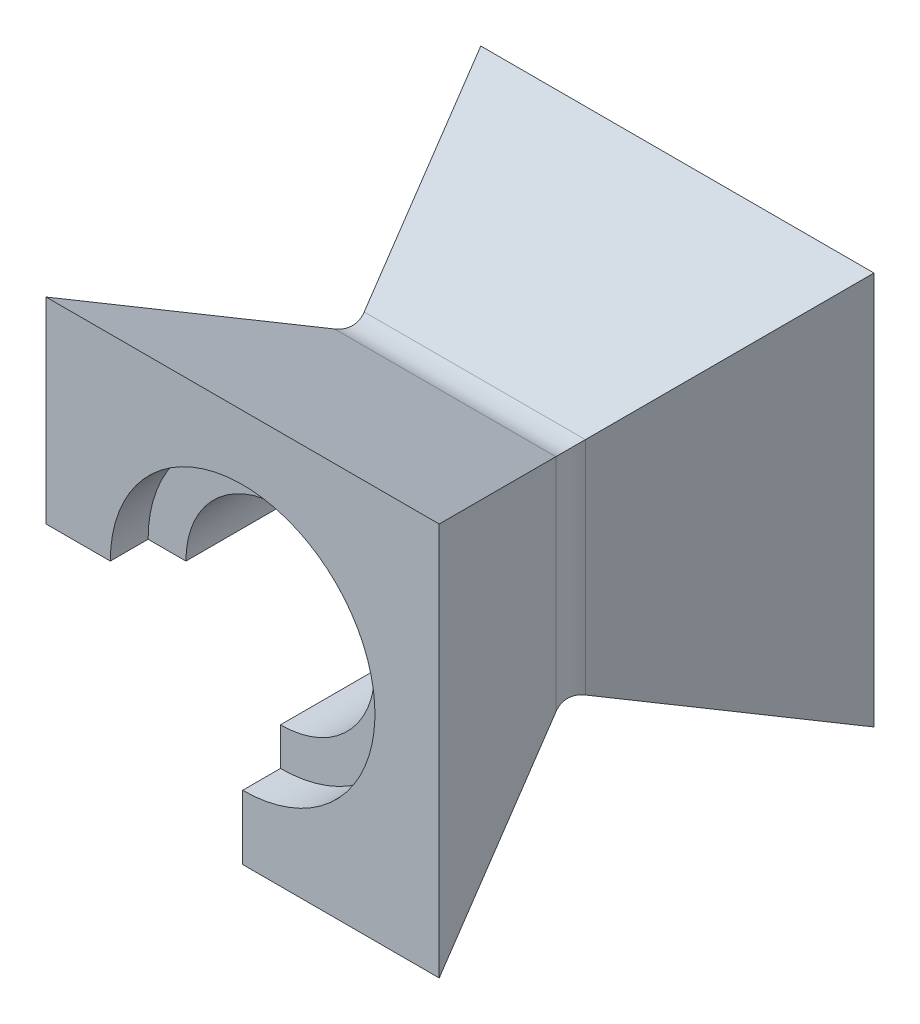
SolidWorks part; units mm, degrees
material "Cast Stainless Steel"
ref_plane "Front Plane" through (0, 0, 0) normal (0, 0, 1) x (1, 0, 0)
ref_plane "Top Plane" through (0, 0, 0) normal (0, 1, 0) x (1, 0, 0)
ref_plane "Right Plane" through (0, 0, 0) normal (1, 0, 0) x (0, 0, -1)
sketch "Sketch1" plane through (0, 0, 0) normal (0, 0, 1) x (1, 0, 0)
  line L1 (52, -52) -> (-52, -52)
  line L2 (52, -52) -> (52, 52)
  line L3 (52, 52) -> (-52, 52)
  line L4 (-52, -52) -> (-52, 52)
  line L5 (52, -52) -> (-52, 52) construction
  line L6 (52, 52) -> (-52, -52) construction
  circle A0 centre (0, 0) radius 25
  point P0 (0, 0)
  dimension "D3" = 50
  dimension "D1" = 104
  dimension "D2" = 104
extrude "Boss-Extrude1" add sketch "Sketch1" along normal blind 115
sketch "Sketch4" plane through (0, 52, 0) normal (0, 1, 0) x (1, 0, 0)
  line L0 (0, 0) -> (0, -115) construction
  line L1 (52, -115) -> (-52, -115) construction
  line L2 (-52, -57.5) -> (52, -57.5) construction
  line L3 (-52, -115) -> (-52, 0) construction
  line L4 (52, -115) -> (52, 0) construction
  line L5 (-52, 0) -> (-27.5927, -57.5)
  line L6 (-52, 0) -> (-52, -115)
  line L7 (-52, -115) -> (-27.5927, -57.5)
  line L8 (52, -115) -> (27.5927, -57.5)
  line L9 (52, 0) -> (52, -115)
  line L10 (52, 0) -> (27.5927, -57.5)
  dimension "D1" = 23
sketch "Sketch7" plane through (-52, 0, 0) normal (-1, 0, 0) x (0, 0, 1)
  line L0 (0, 0) -> (115, 0) construction
  line L1 (115, 52) -> (115, -52) construction
  line L2 (57.5, 52) -> (57.5, -52) construction
  line L3 (0, 52) -> (115, 52) construction
  line L4 (115, -52) -> (0, -52) construction
  line L5 (0, 52) -> (115, 52)
  line L6 (115, 52) -> (57.5, 27.5927)
  line L7 (57.5, 27.5927) -> (0, 52)
  line L8 (0, -52) -> (115, -52)
  line L9 (57.5, -27.5927) -> (0, -52)
  line L10 (115, -52) -> (57.5, -27.5927)
  dimension "D1" = 23
extrude "Cut-Extrude3" cut sketch "Sketch7" against normal blind 115
extrude "Cut-Extrude4" cut sketch "Sketch4" against normal blind 115
sketch "Sketch8" plane through (0, 0, 0) normal (0, 0, -1) x (-1, 0, 0)
  line L0 (0, 0) -> (63.1814, 0)
  line L1 (63.1814, 0) -> (63.1814, -61.3662)
  line L2 (63.1814, -61.3662) -> (0, -61.3662)
  line L3 (0, -61.3662) -> (0, 0)
extrude "Cut-Extrude5" cut sketch "Sketch8" against normal through all
fillet "Fillet1" radius 10 4 edges at (-27.5927, 13.7963, 57.5) (0, 27.5927, 57.5) (27.5927, 0, 57.5) (13.7963, -27.5927, 57.5)
sketch "Sketch9" plane through (0, 0, 0) normal (0, 0, -1) x (-1, 0, 0)
  circle A0 centre (0, 0) radius 35
  dimension "D1" = 70
sketch "Sketch10" plane through (0, 0, 115) normal (0, 0, 1) x (1, 0, 0)
  circle A0 centre (0, 0) radius 35 construction
  circle A1 centre (0, 0) radius 35
extrude "Cut-Extrude6" cut sketch "Sketch10" against normal blind 10
extrude "Cut-Extrude7" cut sketch "Sketch9" against normal blind 10
equation "\"A\"= 115mm"
equation "\"B\"= 104mm"
equation "\"C\"= 23mm"
